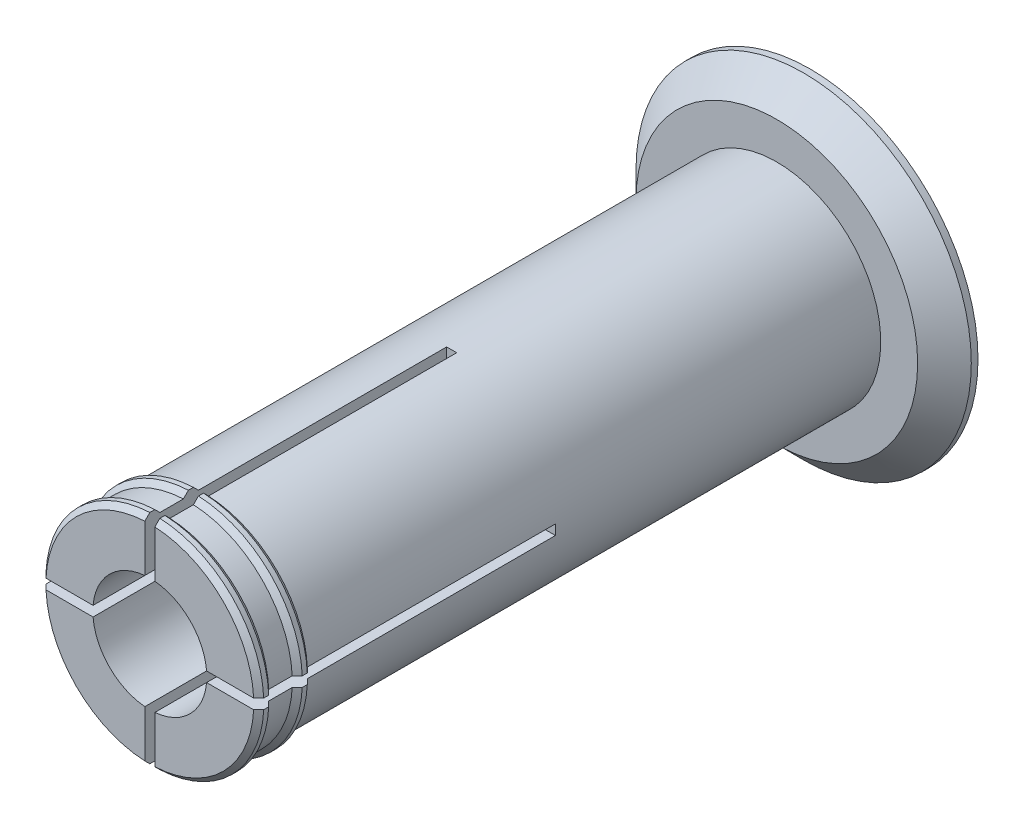
SolidWorks part; units mm, degrees
ref_plane "Front" through (0, 0, 0) normal (0, 0, 1) x (1, 0, 0)
ref_plane "Top" through (0, 0, 0) normal (0, 1, 0) x (1, 0, 0)
ref_plane "Right" through (0, 0, 0) normal (1, 0, 0) x (0, 0, -1)
sketch "Axle base sketch" plane through (0, 0, 0) normal (0, 0, 1) x (1, 0, 0)
  circle A0 centre (0, 0) radius 15.5
  dimension "D1" = 31
extrude "Axle" add sketch "Axle base sketch" along normal blind 93.5
sketch "Guard base" plane through (0, 0, 0) normal (0, 0, -1) x (-1, 0, 0)
  circle A0 centre (0, 0) radius 25
  dimension "D1" = 50
extrude "Guard" add sketch "Guard base" along normal blind 5
sketch "Inner axle hole base" plane through (0, 0, 93.5) normal (0, 0, 1) x (1, 0, 0)
  circle A0 centre (0, 0) radius 8.5
  dimension "D1" = 17
extrude "Inner axle hole" cut sketch "Inner axle hole base" against normal through all
sketch "Mate ring base" plane through (0, 0, 0) normal (0, 1, 0) x (1, 0, 0)
  line L0 (15.5, -93.5) -> (16.25, -92.75)
  line L1 (16.25, -92.75) -> (16.25, -92)
  line L2 (16.25, -92) -> (15.5, -91.25)
  line L3 (16.25, -92.75) -> (16.25, -93.5) construction
  line L4 (16.25, -93.5) -> (15.5, -93.5) construction
  line L5 (15.5, -91.25) -> (15.5, -93.5)
  line L6 (15.5, -93.5) -> (15.5, 0) construction
  line L8 (15.5, -87.75) -> (16.25, -87)
  line L9 (16.25, -87) -> (16.25, -86.25)
  line L10 (16.25, -86.25) -> (15.5, -85.5)
  line L11 (15.5, -85.5) -> (15.5, -87.75)
  dimension "D1" = 0.75
  dimension "D2" = 0.75
  dimension "D3" = 5
  dimension "D4" = 0.75
ref_axis "Center Z" through (0, 0, 0) along (0, 0, -1)
revolve "Mate rings" add sketch "Mate ring base" angle 360 about axis through (0, 0, 0) along (0, 0, -1)
sketch "Bend room base" plane through (0, 0, 93.5) normal (0, 0, 1) x (1, 0, 0)
  line L0 (0.75, -25) -> (0.75, 25)
  line L1 (0.75, 25) -> (-0.75, 25)
  line L2 (-0.75, 25) -> (-0.75, -25)
  line L3 (-0.75, -25) -> (0.75, -25)
  dimension "D1" = 0.75
  dimension "D2" = 0.75
  dimension "D3" = 25
  dimension "D4" = 25
extrude "Bend room 1" cut sketch "Bend room base" against normal blind 45
pattern_circular "Bend room 2" count 2 every 90 about axis through (0, 0, 0) along (0, 0, -1) of "Bend room 1"
chamfer "Easy removal chamfer" distance 4 angle 45 1 edges at (-25, 0, 0)
equation "\"32_92_spool_inner_diameter\"=32"
equation "\"D1@Axle base sketch\"=\"32_92_spool_inner_diameter\"- \"spool_inner_diameter_room\""
equation "\"spool_inner_diameter_room\"=1"
equation "\"32_92_spool_thickness\"=92"
equation "\"D1@Axle\"=\"32_92_spool_thickness\"+\"guard_thickness\"+\"removal_room\"*2 + \"32_92_extra_spool_thickness\""
equation "\"32_92_guard_diameter\"=50"
equation "\"D1@Guard base\"=\"32_92_guard_diameter\""
equation "\"guard_thickness\"=5"
equation "\"D1@Guard\"=\"guard_thickness\""
equation "\"large_inner_axle_diameter\"=20"
equation "\"D1@Inner axle hole base\"=\"small_inner_axle_diameter\""
equation "\"mate_room\"= 0.25"
equation "\"removal_room\"= 0.75"
equation "\"small_inner_axle_diameter\"=17"
equation "\"53_55_spool_inner_diameter\"=53"
equation "\"53_55_spool_thickness\"=55"
equation "\"53_55_guard_diameter\"=75"
equation "\"53_55_coupling_tooth_height\"=27"
equation "\"53_55_coupling_tooth_thickness_total\"=8"
equation "\"53_55_coupling_tooth_protrusion\"=1.5"
equation "\"53_55_coupling_tooth_head_height\"=7.5"
equation "\"53_55_coupling_tooth_depth\"=10"
equation "\"53_55_coupling_tooth_base_thickness\"=9.5"
equation "\"D1@Mate ring base\"=\"removal_room\""
equation "\"D2@Mate ring base\"=\"removal_room\""
equation "\"D3@Mate ring base\"=\"guard_thickness\""
equation "\"D4@Mate ring base\"=\"removal_room\""
equation "\"D1@Bend room base\" = \"removal_room\""
equation "\"D2@Bend room base\"=\"removal_room\""
equation "\"D3@Bend room base\"=\"32_92_guard_diameter\"/2"
equation "\"D4@Bend room base\"=\"32_92_guard_diameter\"/2"
equation "\"bend_room_length_multiplier\"=3"
equation "\"D1@Bend room 1\"=\"bend_room_length_multiplier\"*(\"32_92_spool_inner_diameter\"-\"small_inner_axle_diameter\")"
equation "\"D1@Easy removal chamfer\"=\"guard_thickness\"-1"
equation "\"32_92_extra_spool_thickness\"=-5"
